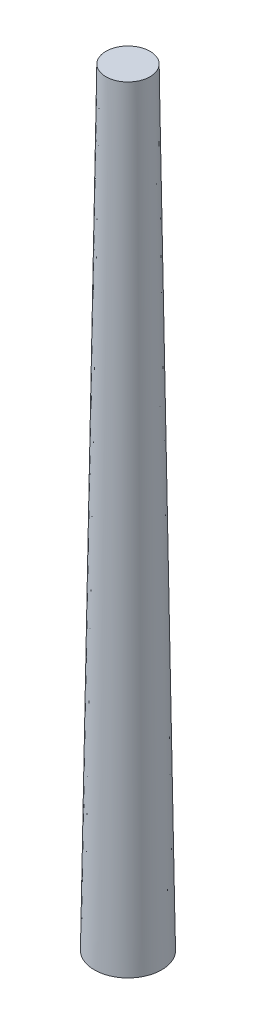
SolidWorks part; units mm, degrees
ref_plane "Front Plane" through (0, 0, 0) normal (0, 0, 1) x (1, 0, 0)
ref_plane "Top Plane" through (0, 0, 0) normal (0, 1, 0) x (1, 0, 0)
ref_plane "Right Plane" through (0, 0, 0) normal (1, 0, 0) x (0, 0, -1)
sketch "Sketch1" plane through (0, 0, 0) normal (0, 0, 1) x (1, 0, 0)
  line L0 (0, 0) -> (6.5405, 0)
  line L1 (6.5405, 0) -> (4.2862, 149.225)
  line L2 (4.2862, 149.225) -> (0, 149.225)
  line L3 (0, 149.225) -> (0, 0)
  dimension "D1" = 6.5405
  dimension "D2" = 4.2862
  dimension "D3" = 149.225
revolve "Revolve1" add sketch "Sketch1" angle 360 about L3
